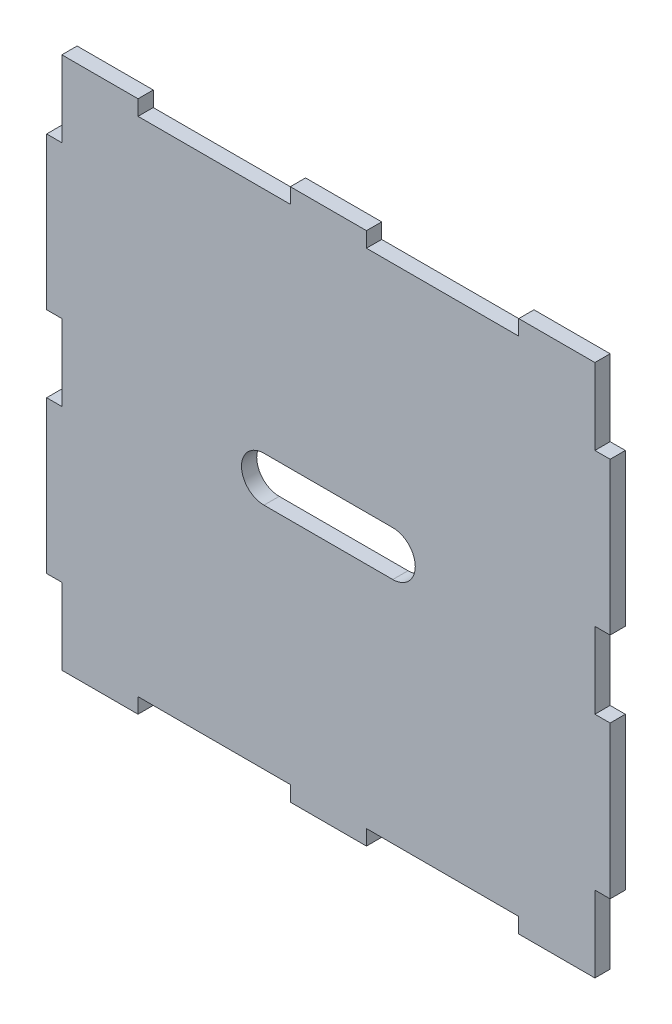
SolidWorks part; units mm, degrees
ref_plane "Front Plane" through (0, 0, 0) normal (0, 0, 1) x (1, 0, 0)
ref_plane "Top Plane" through (0, 0, 0) normal (0, 1, 0) x (1, 0, 0)
ref_plane "Right Plane" through (0, 0, 0) normal (1, 0, 0) x (0, 0, -1)
sketch "Sketch1" plane through (0, 0, 0) normal (0, 0, 1) x (1, 0, 0)
  line L1 (-35, -35) -> (35, -35)
  line L2 (-35, -35) -> (-35, 35)
  line L3 (-35, 35) -> (35, 35)
  line L4 (35, -35) -> (35, 35)
  line L5 (0, 35) -> (0, -35) construction
  line L6 (-35, 0) -> (35, 0) construction
  line L11 (0, 18) -> (0, -18) construction
  line L12 (-17.25, 0) -> (17.25, 0) construction
  point P0 (0, 0)
  point P4 (0, 0)
  dimension "D1" = 70
  dimension "D2" = 70
extrude "Boss-Extrude1" add sketch "Sketch1" against normal blind 2
sketch "Sketch2" plane through (0, 0, 0) normal (0, 0, 1) x (1, 0, 0)
  line L0 (-35, 35) -> (-25, 35)
  line L1 (35, 35) -> (-35, 35) construction
  line L2 (-25, 35) -> (-5, 35)
  line L3 (-5, 35) -> (5, 35)
  line L4 (5, 35) -> (25, 35)
  line L6 (35, 35) -> (35, 25)
  line L7 (-25, 33) -> (-5, 33)
  line L8 (-25, 33) -> (-25, 37)
  line L9 (-25, 37) -> (-5, 37)
  line L10 (-5, 33) -> (-5, 37)
  line L11 (-15, 37) -> (-15, 33) construction
  line L12 (-25, 35) -> (-5, 35) construction
  line L13 (5, 33) -> (25, 33)
  line L14 (5, 33) -> (5, 37)
  line L15 (5, 37) -> (25, 37)
  line L16 (25, 33) -> (25, 37)
  line L17 (15, 37) -> (15, 33) construction
  line L18 (5, 35) -> (25, 35) construction
  line L19 (35, -35) -> (35, 35) construction
  line L20 (35, 25) -> (35, 5)
  line L21 (35, 5) -> (35, -5)
  line L22 (35, -5) -> (35, -25)
  line L23 (-35, -35) -> (-25, -35)
  line L24 (35, -5) -> (33, -5)
  line L25 (35, -5) -> (35, -25)
  line L26 (35, -25) -> (33, -25)
  line L27 (33, -5) -> (33, -25)
  line L28 (35, 25) -> (33, 25)
  line L29 (35, 25) -> (35, 5)
  line L30 (35, 5) -> (33, 5)
  line L31 (33, 25) -> (33, 5)
  line L32 (-35, -35) -> (35, -35) construction
  line L33 (-25, -35) -> (-5, -35)
  line L34 (-5, -35) -> (5, -35)
  line L35 (5, -35) -> (25, -35)
  line L36 (-35, 35) -> (-35, 25)
  line L37 (-25, -35) -> (-5, -35)
  line L38 (-25, -35) -> (-25, -33)
  line L39 (-25, -33) -> (-5, -33)
  line L40 (-5, -35) -> (-5, -33)
  line L41 (5, -35) -> (25, -35)
  line L42 (5, -35) -> (5, -33)
  line L43 (5, -33) -> (25, -33)
  line L44 (25, -35) -> (25, -33)
  line L45 (-35, 35) -> (-35, -35) construction
  line L46 (-35, 25) -> (-35, 5)
  line L47 (-35, 5) -> (-35, -5)
  line L48 (-35, -5) -> (-35, -25)
  line L49 (-35, 25) -> (-37, 25)
  line L50 (-35, 25) -> (-33, 25)
  line L51 (-35, 25) -> (-35, 5)
  line L52 (-35, 5) -> (-33, 5)
  line L53 (-33, 25) -> (-33, 5)
  line L54 (-35, -5) -> (-33, -5)
  line L55 (-35, -5) -> (-35, -25)
  line L56 (-35, -25) -> (-33, -25)
  line L57 (-33, -5) -> (-33, -25)
  line L58 (-35, 25) -> (-35, 5)
  line L59 (-35, 5) -> (-37, 5)
  line L60 (-37, 25) -> (-37, 5)
  line L61 (-35, -5) -> (-37, -5)
  line L62 (-35, -5) -> (-35, -25)
  line L63 (-35, -25) -> (-37, -25)
  line L64 (-37, -5) -> (-37, -25)
  line L65 (-25, -35) -> (-5, -35)
  line L66 (-25, -35) -> (-25, -37)
  line L67 (-25, -37) -> (-5, -37)
  line L68 (-5, -35) -> (-5, -37)
  line L69 (5, -35) -> (25, -35)
  line L70 (5, -35) -> (5, -37)
  line L71 (5, -37) -> (25, -37)
  line L72 (25, -35) -> (25, -37)
  line L73 (35, -25) -> (37, -25)
  line L74 (35, -25) -> (35, -5)
  line L75 (35, -5) -> (37, -5)
  line L76 (37, -25) -> (37, -5)
  line L77 (35, 5) -> (37, 5)
  line L78 (35, 5) -> (35, 25)
  line L79 (35, 25) -> (37, 25)
  line L80 (37, 5) -> (37, 25)
  point P7 (15, 35)
  point P9 (-15, 35)
  point P10 (-15, 35)
  point P14 (15, 35)
  line M25 (35, -35) -> (35, 35)
  line M27 (-35, 35) -> (-35, -35)
  dimension "D1" = 10
  dimension "D2" = 20
  dimension "D3" = 10
  dimension "D4" = 20
  dimension "D5" = 4
  dimension "D6" = 20
  dimension "D7" = 20
  dimension "D8" = 4
  dimension "D9" = 10
  dimension "D10" = 20
  dimension "D11" = 10
  dimension "D12" = 20
  dimension "D13" = 2
  dimension "D14" = 2
  dimension "D15" = 10
  dimension "D16" = 20
  dimension "D17" = 10
  dimension "D18" = 20
  dimension "D19" = 20
  dimension "D20" = 20
  dimension "D21" = 2
  dimension "D22" = 2
  dimension "D23" = 10
  dimension "D24" = 20
  dimension "D25" = 10
  dimension "D26" = 20
  dimension "D27" = 2
  dimension "D28" = 2
  dimension "D29" = 2
  dimension "D30" = 2
  dimension "D31" = 2
  dimension "D32" = 2
  dimension "D33" = 2
  dimension "D34" = 2
sketch "Sketch3" plane through (0, 0, 0) normal (0, 0, 1) x (1, 0, 0)
  line L0 (-35, 35) -> (-25, 35)
  line L2 (-25, 35) -> (-5, 35)
  line L3 (-5, 35) -> (5, 35)
  line L4 (5, 35) -> (25, 35)
  line L6 (35, 35) -> (35, 25)
  line L7 (-25, 33) -> (-5, 33)
  line L8 (-25, 33) -> (-25, 37)
  line L9 (-25, 37) -> (-5, 37)
  line L10 (-5, 33) -> (-5, 37)
  line L11 (-15, 37) -> (-15, 33) construction
  line L12 (-25, 35) -> (-5, 35) construction
  line L13 (5, 33) -> (25, 33)
  line L14 (5, 33) -> (5, 37)
  line L15 (5, 37) -> (25, 37)
  line L16 (25, 33) -> (25, 37)
  line L17 (15, 37) -> (15, 33) construction
  line L18 (5, 35) -> (25, 35) construction
  line L20 (35, 25) -> (35, 5)
  line L21 (35, 5) -> (35, -5)
  line L22 (35, -5) -> (35, -25)
  line L23 (-35, -35) -> (-25, -35)
  line L24 (35, -5) -> (33, -5)
  line L25 (35, -5) -> (35, -25)
  line L26 (35, -25) -> (33, -25)
  line L27 (33, -5) -> (33, -25)
  line L28 (35, 25) -> (33, 25)
  line L29 (35, 25) -> (35, 5)
  line L30 (35, 5) -> (33, 5)
  line L31 (33, 25) -> (33, 5)
  line L33 (-25, -35) -> (-5, -35)
  line L34 (-5, -35) -> (5, -35)
  line L35 (5, -35) -> (25, -35)
  line L36 (-35, 35) -> (-35, 25)
  line L37 (-25, -35) -> (-5, -35)
  line L38 (-25, -35) -> (-25, -33)
  line L39 (-25, -33) -> (-5, -33)
  line L40 (-5, -35) -> (-5, -33)
  line L41 (5, -35) -> (25, -35)
  line L42 (5, -35) -> (5, -33)
  line L43 (5, -33) -> (25, -33)
  line L44 (25, -35) -> (25, -33)
  line L46 (-35, 25) -> (-35, 5)
  line L47 (-35, 5) -> (-35, -5)
  line L48 (-35, -5) -> (-35, -25)
  line L49 (-35, 25) -> (-37, 25)
  line L50 (-35, 25) -> (-33, 25)
  line L51 (-35, 25) -> (-35, 5)
  line L52 (-35, 5) -> (-33, 5)
  line L53 (-33, 25) -> (-33, 5)
  line L54 (-35, -5) -> (-33, -5)
  line L55 (-35, -5) -> (-35, -25)
  line L56 (-35, -25) -> (-33, -25)
  line L57 (-33, -5) -> (-33, -25)
  line L58 (-35, 25) -> (-35, 5)
  line L59 (-35, 5) -> (-37, 5)
  line L60 (-37, 25) -> (-37, 5)
  line L61 (-35, -5) -> (-37, -5)
  line L62 (-35, -5) -> (-35, -25)
  line L63 (-35, -25) -> (-37, -25)
  line L64 (-37, -5) -> (-37, -25)
  line L65 (-25, -35) -> (-5, -35)
  line L66 (-25, -35) -> (-25, -37)
  line L67 (-25, -37) -> (-5, -37)
  line L68 (-5, -35) -> (-5, -37)
  line L69 (5, -35) -> (25, -35)
  line L70 (5, -35) -> (5, -37)
  line L71 (5, -37) -> (25, -37)
  line L72 (25, -35) -> (25, -37)
  line L73 (35, -25) -> (37, -25)
  line L74 (35, -25) -> (35, -5)
  line L75 (35, -5) -> (37, -5)
  line L76 (37, -25) -> (37, -5)
  line L77 (35, 5) -> (37, 5)
  line L78 (35, 5) -> (35, 25)
  line L79 (35, 25) -> (37, 25)
  line L80 (37, 5) -> (37, 25)
  point P7 (15, 35)
  point P9 (-15, 35)
  point P10 (-15, 35)
  point P14 (15, 35)
  dimension "D1" = 10
  dimension "D2" = 20
  dimension "D3" = 10
  dimension "D4" = 20
  dimension "D5" = 4
  dimension "D6" = 20
  dimension "D7" = 20
  dimension "D8" = 4
  dimension "D9" = 10
  dimension "D10" = 20
  dimension "D11" = 10
  dimension "D12" = 20
  dimension "D13" = 2
  dimension "D14" = 2
  dimension "D15" = 10
  dimension "D16" = 20
  dimension "D17" = 10
  dimension "D18" = 20
  dimension "D19" = 20
  dimension "D20" = 20
  dimension "D21" = 2
  dimension "D22" = 2
  dimension "D23" = 10
  dimension "D24" = 20
  dimension "D25" = 10
  dimension "D26" = 20
  dimension "D27" = 2
  dimension "D28" = 2
  dimension "D29" = 2
  dimension "D30" = 2
  dimension "D31" = 2
  dimension "D32" = 2
  dimension "D33" = 2
  dimension "D34" = 2
extrude "Boss-Extrude2" add sketch "Sketch2" against normal blind 2 contours L49 L60 L59 M27 | L61 L64 L63 M27 | L73 L76 L75 M25 | L77 L80 L79 M25
extrude "Cut-Extrude1" cut sketch "Sketch3" against normal blind 2 contours L7 L10 L2 L8 | L13 L16 L4 L14 | L33 L40 L39 L38 | L35 L44 L43 L42
sketch "Sketch4" plane through (0, 0, 0) normal (0, 0, 1) x (1, 0, 0)
  line L1 (-8.46, -2.95) -> (8.46, -2.95)
  line L2 (-8.46, -2.95) -> (-8.46, 2.95)
  line L3 (-8.46, 2.95) -> (8.46, 2.95)
  line L4 (8.46, -2.95) -> (8.46, 2.95)
  line L5 (0, 2.95) -> (0, -2.95) construction
  line L6 (-8.46, 0) -> (8.46, 0) construction
  arc A0 (8.46, 2.95) -> (8.46, -2.95) centre (8.46, 0) cw
  arc A1 (-8.46, 2.95) -> (-8.46, -2.95) centre (-8.46, 0) ccw
  point P0 (0, 0)
  dimension "D1" = 16.92
  dimension "D2" = 5.9
extrude "Cut-Extrude2" cut sketch "Sketch4" against normal blind 10 contours L1 L4 L3 L2 | A0 L4 | L2 A1
